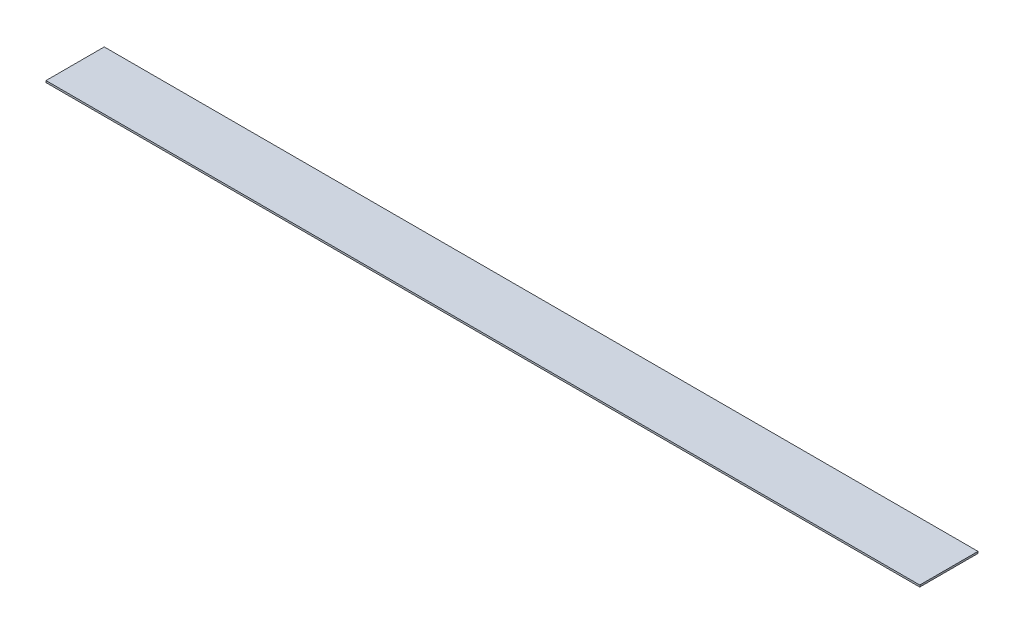
SolidWorks part; units mm, degrees
ref_plane "Front Plane" through (0, 0, 0) normal (0, 0, 1) x (1, 0, 0)
ref_plane "Top Plane" through (0, 0, 0) normal (0, 1, 0) x (1, 0, 0)
ref_plane "Right Plane" through (0, 0, 0) normal (1, 0, 0) x (0, 0, -1)
sketch "Sketch1" plane through (0, 0, 0) normal (0, 1, 0) x (1, 0, 0)
  line L1 (0, 0) -> (762, 0)
  line L2 (0, 0) -> (0, 50.8)
  line L3 (0, 50.8) -> (762, 50.8)
  line L4 (762, 0) -> (762, 50.8)
  dimension "D1" = 50.8
  dimension "D2" = 762
extrude "Boss-Extrude1" add sketch "Sketch1" along normal blind 1.5875
